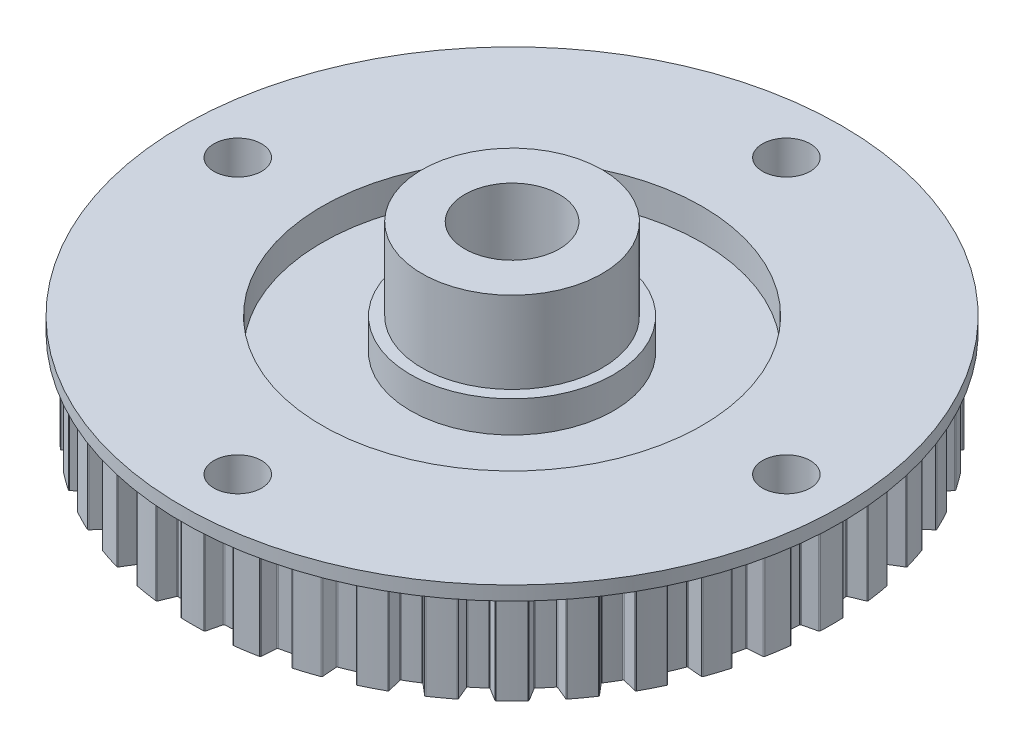
SolidWorks part; units mm, degrees
ref_plane "Front Plane" through (0, 0, 0) normal (0, 0, 1) x (1, 0, 0)
ref_plane "Top Plane" through (0, 0, 0) normal (0, 1, 0) x (1, 0, 0)
ref_plane "Right Plane" through (0, 0, 0) normal (1, 0, 0) x (0, 0, -1)
sketch "Sketch1" plane through (0, 0, 0) normal (0, 0, 1) x (1, 0, 0)
  line L0 (0, 0) -> (0, 17.82) construction
  line L1 (0, 0) -> (4.75, 0) construction
  line L2 (4.75, 0) -> (4.75, 19)
  line L3 (4.75, 19) -> (9.05, 19)
  line L4 (9.05, 19) -> (9.05, 10.8)
  line L5 (9.05, 10.8) -> (10.2, 10.8)
  line L6 (10.2, 10.8) -> (10.2, 7.65)
  line L7 (10.2, 7.65) -> (19.075, 7.65)
  line L8 (19.075, 7.65) -> (19.075, 10.8)
  line L9 (19.075, 10.8) -> (33.1, 10.8)
  line L10 (33.1, 10.8) -> (33.1, 9.4)
  line L11 (33.1, 9.4) -> (30.55, 9.4)
  line L12 (30.55, 9.4) -> (30.55, 0)
  line L13 (30.55, 0) -> (25.125, 0)
  line L14 (25.125, 0) -> (25.125, 3.6)
  line L15 (25.125, 3.6) -> (12.65, 3.6)
  line L16 (12.65, 3.6) -> (12.65, 0)
  line L17 (12.65, 0) -> (4.75, 0)
  point P23 (10.2, 9.225)
  dimension "D1" = 3.6
  dimension "D2" = 19
  dimension "D3" = 8.2
  dimension "D4" = 3.15
  dimension "D5" = 1.4
  dimension "D6" = 66.2
  dimension "D7" = 9.5
  dimension "D8" = 18.1
  dimension "D9" = 20.4
  dimension "D10" = 25.3
  dimension "D11" = 50.25
  dimension "D12" = 38.15
  dimension "D13" = 61.1
revolve "Revolve1" add sketch "Sketch1" angle 360 about L0
sketch "Sketch2" plane through (0, 10.8, 0) normal (0, 1, 0) x (1, 0, 0)
  line L0 (-29.95, 0) -> (29.95, 0) construction
  circle A0 centre (0, 0) radius 27.55 construction
  circle A1 centre (-27.55, 0) radius 2.4
  circle A2 centre (0, 27.55) radius 2.4
  circle A3 centre (27.55, 0) radius 2.4
  circle A4 centre (0, -27.55) radius 2.4
  dimension "D1" = 59.9
  dimension "D2" = 4.8
extrude "Cut-Extrude4" cut sketch "Sketch2" against normal up to next
sketch "Sketch3" plane through (0, 0, 0) normal (0, -1, 0) x (1, 0, 0)
  line L0 (0, 27.55) -> (0, 32.1) construction
  line L1 (1.2, 32.0776) -> (1.575, 30.5094)
  line L2 (-1.2, 32.0776) -> (-1.575, 30.5094)
  circle A0 centre (0, 0) radius 30.55
  circle A2 centre (0, 0) radius 32.1
  circle A4 centre (0, 27.55) radius 2.4 construction
  circle A5 centre (0, 27.55) radius 2.4 construction
  circle M9 centre (0, 0) radius 30.55
  dimension "D2" = 61.1
  dimension "D5" = 64.2
  dimension "D3" = 2.4
  dimension "D4" = 3.15
extrude "Boss-Extrude1" add sketch "Sketch3" against normal up to next (9.4 mm away) contours L1 A2 L2 M9
fillet "Fillet1" radius 0.1 4 edges at (-1.575, 4.7, 30.5094) (-1.2, 4.7, 32.0776) (1.575, 4.7, 30.5094) (1.2, 4.7, 32.0776)
pattern_circular "CirPattern1" count 40 over 360 about axis through (0, 0, 0) along (0, 1, 0) of "Boss-Extrude1", "Fillet1"
